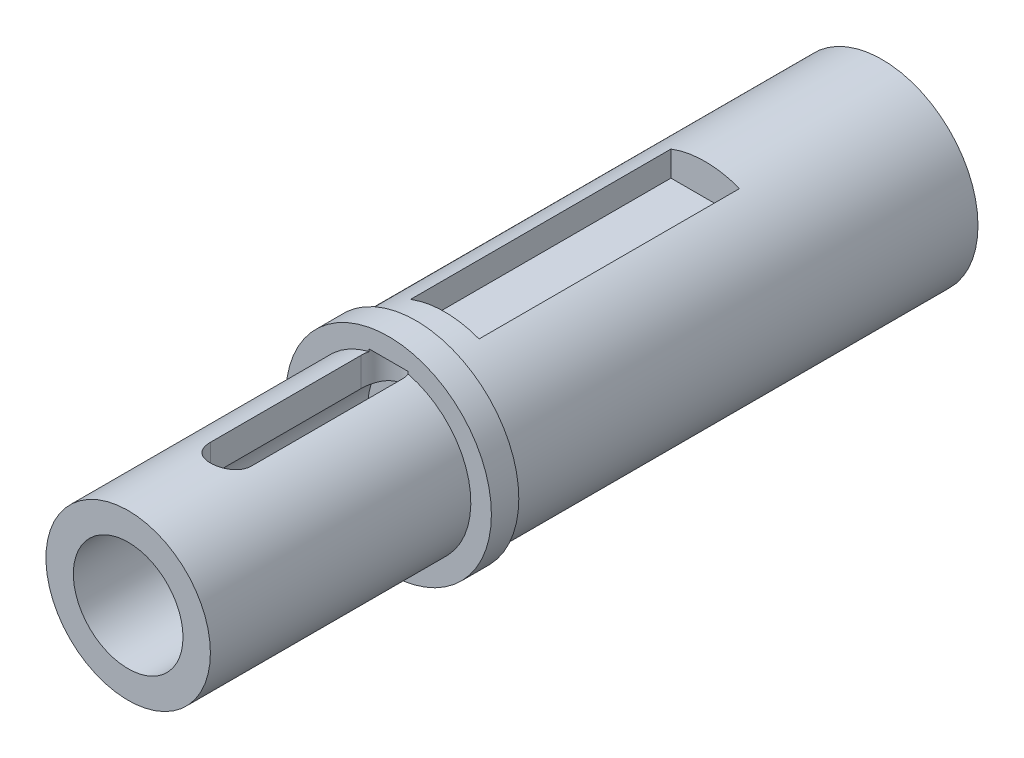
SolidWorks part; units mm, degrees
ref_plane "Front Plane" through (0, 0, 0) normal (0, 0, 1) x (1, 0, 0)
ref_plane "Top Plane" through (0, 0, 0) normal (0, 1, 0) x (1, 0, 0)
ref_plane "Right Plane" through (0, 0, 0) normal (1, 0, 0) x (0, 0, -1)
sketch "Sketch1" plane through (0, 0, 0) normal (0, 0, 1) x (1, 0, 0)
  circle A0 centre (0, 0) radius 7
  dimension "D1" = 14
extrude "Boss-Extrude1" add sketch "Sketch1" along normal blind 34
sketch "Sketch2" plane through (0, 0, 34) normal (0, 0, 1) x (1, 0, 0)
  circle A0 centre (0, 0) radius 7.5
  dimension "D1" = 15
extrude "Boss-Extrude2" add sketch "Sketch2" along normal blind 2
sketch "Sketch3" plane through (0, 0, 36) normal (0, 0, 1) x (1, 0, 0)
  circle A0 centre (0, 0) radius 6
  dimension "D1" = 12
extrude "Boss-Extrude3" add sketch "Sketch3" along normal blind 19
sketch "Sketch4" plane through (0, 0, 55) normal (0, 0, 1) x (1, 0, 0)
  circle A0 centre (0, 0) radius 4
  dimension "D1" = 8
extrude "Cut-Extrude1" cut sketch "Sketch4" against normal blind 21.5
ref_plane "Plane2" through (0, 6, 0) normal (0, 1, 0) x (1, 0, 0)
sketch "Sketch5" plane through (0, 6, 0) normal (0, 1, 0) x (1, 0, 0)
  line L0 (0, -47.5) -> (0, -36.5) construction
  line L1 (0, -8.25) -> (0, 8.25) construction
  line L2 (-1.5, -47.5) -> (-1.5, -36.5)
  line L3 (1.5, -47.5) -> (1.5, -36.5)
  line L4 (-13.8465, -35) -> (13.3291, -35)
  line L5 (0, -49) -> (17.8496, -49)
  line L6 (-6, -55) -> (6, -55) construction
  arc A0 (-1.5, -47.5) -> (1.5, -47.5) centre (0, -47.5) ccw
  arc A1 (1.5, -36.5) -> (-1.5, -36.5) centre (0, -36.5) ccw
  point P5 (0, -42)
  dimension "D1" = 6
  dimension "D2" = 14
  dimension "D3" = 3
extrude "Cut-Extrude2" cut sketch "Sketch5" against normal up to next
ref_plane "Plane3" through (0, 0, 31.9) normal (0, 0, -1) x (-1, 0, 0)
sketch "Sketch6" plane through (0, 0, 31.9) normal (0, 0, -1) x (-1, 0, 0)
  line L1 (-2.5, 4.7) -> (2.5, 4.7)
  line L2 (-2.5, 4.7) -> (-2.5, 9.3)
  line L3 (-2.5, 9.3) -> (2.5, 9.3)
  line L4 (2.5, 4.7) -> (2.5, 9.3)
  line L5 (-2.5, 4.7) -> (2.5, 9.3) construction
  line L6 (-2.5, 9.3) -> (2.5, 4.7) construction
  circle A0 centre (0, 0) radius 7 construction
  point P0 (0, 7)
  point P7 (0, 0)
  dimension "D1" = 5
  dimension "D2" = 9.3
extrude "Cut-Extrude3" cut sketch "Sketch6" along normal blind 19
